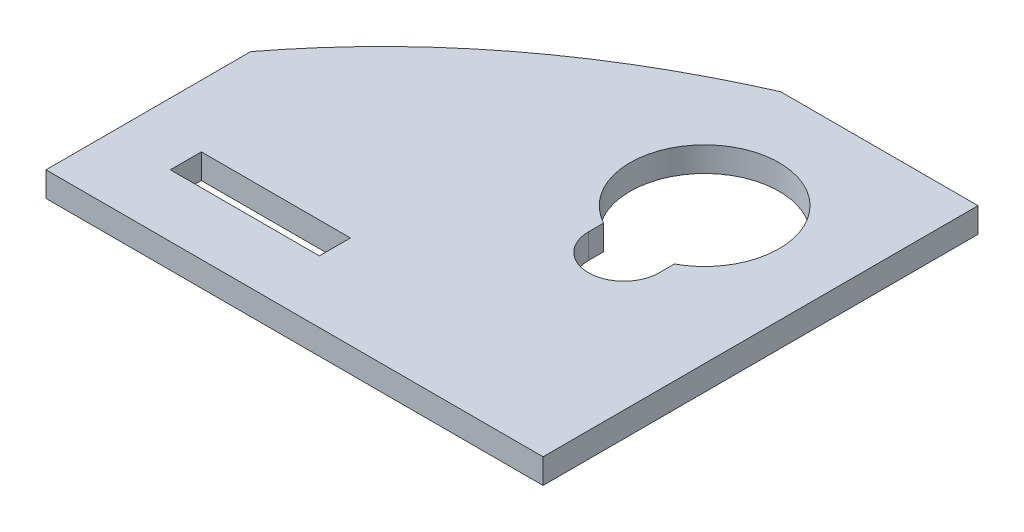
SolidWorks part; units mm, degrees
ref_plane "Plan de face" through (0, 0, 0) normal (0, 0, 1) x (1, 0, 0)
ref_plane "Plan de dessus" through (0, 0, 0) normal (0, 1, 0) x (1, 0, 0)
ref_plane "Plan de droite" through (0, 0, 0) normal (1, 0, 0) x (0, 0, -1)
sketch "Esquisse1" plane through (0, 0, 0) normal (0, 1, 0) x (1, 0, 0)
  line L0 (9, 15.1151) -> (9, -20.8368) construction
  line L1 (-20, -17.5) -> (20, -17.5)
  line L2 (-20, -17.5) -> (-20, 17.5)
  line L3 (-20, 17.5) -> (20, 17.5)
  line L4 (20, -17.5) -> (20, 17.5)
  line L5 (-20, -17.5) -> (20, 17.5) construction
  line L6 (-20, 17.5) -> (20, -17.5) construction
  line L7 (6.15, 1.2201) -> (6.15, 0)
  line L8 (11.85, 1.2201) -> (11.85, 0)
  line L10 (-15, -12.5) -> (-3, -12.5)
  line L11 (-15, -12.5) -> (-15, -10)
  line L12 (-15, -10) -> (-3, -10)
  line L13 (-3, -12.5) -> (-3, -10)
  arc A0 (11.85, 1.2201) -> (6.15, 1.2201) centre (9, 6.5) ccw
  arc A1 (6.15, 0) -> (11.85, 0) centre (9, 0) ccw
  point P0 (0, 0)
  dimension "D1" = 12
  dimension "D2" = 5.7
  dimension "D3" = 6.5
  dimension "D4" = 2.5
  dimension "D5" = 12
  dimension "D6" = 5
  dimension "D7" = 5
  dimension "D8" = 11
  dimension "D9" = 11
  dimension "D10" = 40
  dimension "D11" = 35
extrude "Boss.-Extru.1" add sketch "Esquisse1" along normal blind 2
sketch "Esquisse2" plane through (0, 2, 0) normal (0, 1, 0) x (1, 0, 0)
  line L0 (20, 17.5) -> (-20, 17.5) construction
  line L1 (-20, 17.5) -> (-20, -17.5) construction
  line L2 (-28.7452, -17.5) -> (-25.6331, 26.5529)
  line L3 (-25.6331, 26.5529) -> (4.1166, 17.5)
  spline S0 degree 2 poles (4.1166, 17.5) (-20.2629, 6.7207) (-28.7452, -17.5) knots 0 0 0 1 1 1
extrude "Enlèv. mat.-Extru.1" cut sketch "Esquisse2" against normal blind 10
